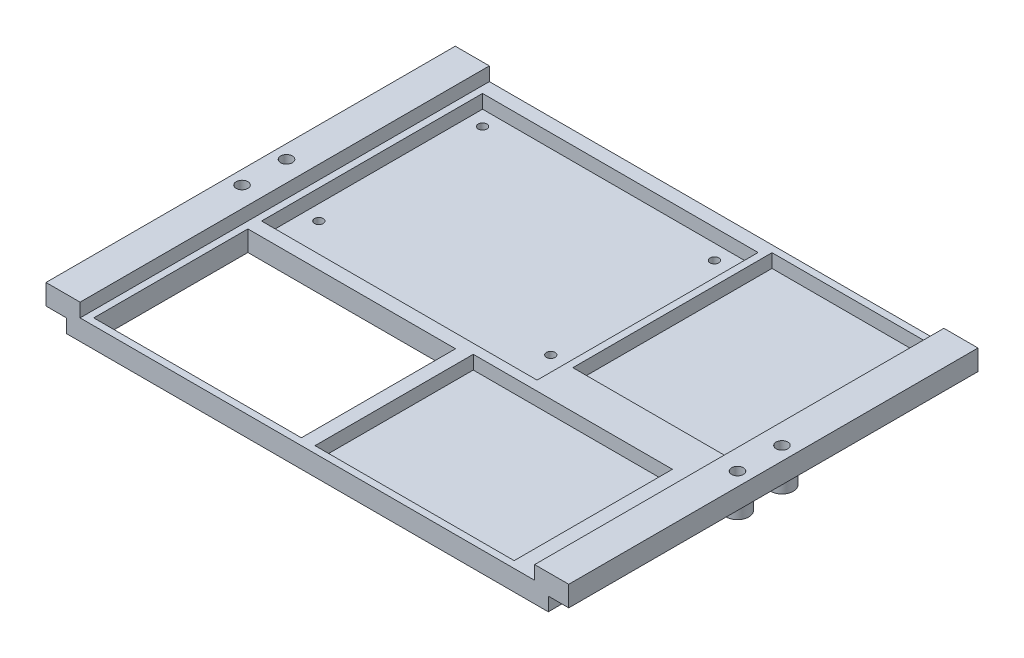
SolidWorks part; units mm, degrees
ref_plane "Front Plane" through (0, 0, 0) normal (0, 0, 1) x (1, 0, 0)
ref_plane "Top Plane" through (0, 0, 0) normal (0, 1, 0) x (1, 0, 0)
ref_plane "Right Plane" through (0, 0, 0) normal (1, 0, 0) x (0, 0, -1)
sketch "Sketch2" plane through (0, 0, 0) normal (0, 0, 1) x (1, 0, 0)
  line L0 (179.1, 12.5) -> (191.6, 12.5)
  line L1 (7.5, 0) -> (184.1, 0)
  line L2 (0, 5) -> (0, 12.5)
  line L3 (0, 12.5) -> (12.5, 12.5)
  line L4 (191.6, 5) -> (191.6, 12.5)
  line L7 (0, 5) -> (7.5, 5)
  line L8 (7.5, 0) -> (7.5, 5)
  line L11 (191.6, 5) -> (184.1, 5)
  line L12 (184.1, 0) -> (184.1, 5)
  line L14 (12.5, 12.5) -> (12.5, 7.5)
  line L15 (12.5, 7.5) -> (179.1, 7.5)
  line L16 (179.1, 12.5) -> (179.1, 7.5)
  dimension "D1" = 191.6
  dimension "D2" = 5
  dimension "D3" = 5
  dimension "D4" = 5
  dimension "D5" = 12.5
  dimension "D6" = 7.5
  dimension "D7" = 7.5
  dimension "D8" = 12.5
  dimension "D9" = 12.5
extrude "PlateFrame" add sketch "Sketch2" along normal blind 150
sketch "Sketch3" plane through (0, 12.5, 0) normal (0, 1, 0) x (1, 0, 0)
  line L0 (12.5, 0) -> (0, 0) construction
  line L2 (0, -150) -> (0, 0) construction
  line L3 (191.6, -150) -> (191.6, 0) construction
  line L4 (191.6, 0) -> (179.1, 0) construction
  circle A0 centre (5, -66.85) radius 2.15
  circle A1 centre (5, -83.15) radius 2.15
  circle A2 centre (186.6, -66.85) radius 2.15
  circle A3 centre (186.6, -83.15) radius 2.15
  dimension "D1" = 4.3
  dimension "D2" = 4.3
  dimension "D3" = 4.3
  dimension "D4" = 4.3
  dimension "D5" = 66.85
  dimension "D6" = 16.3
  dimension "D7" = 5
  dimension "D8" = 5
  dimension "D9" = 5
  dimension "D10" = 181.6
  dimension "D11" = 66.85
  dimension "D12" = 16.3
extrude "HoleSupport" cut sketch "Sketch3" against normal blind 7.5
sketch "Sketch4" plane through (0, 12.5, 0) normal (0, 1, 0) x (1, 0, 0)
  circle A0 centre (5, -66.85) radius 2.15
  circle A1 centre (5, -83.15) radius 2.15
  circle A2 centre (186.6, -83.15) radius 2.15
  circle A3 centre (186.6, -66.85) radius 2.15
  circle A4 centre (186.6, -66.85) radius 4.15
  circle A5 centre (186.6, -83.15) radius 4.15
  circle A6 centre (5, -66.85) radius 4.15
  circle A7 centre (5, -83.15) radius 4.15
  dimension "D1" = 2
extrude "CylindricalSupports" add sketch "Sketch4" against normal blind 12.5
sketch "Sketch5" plane through (0, 7.5, 0) normal (0, 1, 0) x (1, 0, 0)
  line L2 (12.5, -150) -> (12.5, 0) construction
  line L3 (15, -5) -> (116, -5)
  line L4 (15, -5) -> (15, -86)
  line L5 (15, -86) -> (116, -86)
  line L6 (116, -5) -> (116, -86)
  line L7 (176.6, -2.5) -> (118.6, -2.5)
  line L8 (176.6, -2.5) -> (176.6, -75.5)
  line L9 (176.6, -75.5) -> (118.6, -75.5)
  line L10 (118.6, -2.5) -> (118.6, -75.5)
  line L11 (169.1, -147.5) -> (96.1, -147.5)
  line L12 (169.1, -147.5) -> (169.1, -89.5)
  line L13 (169.1, -89.5) -> (96.1, -89.5)
  line L14 (96.1, -147.5) -> (96.1, -89.5)
  line L15 (179.1, -150) -> (179.1, 0) construction
  line L16 (179.1, 0) -> (12.5, 0) construction
  line L17 (179.1, -150) -> (12.5, -150) construction
  dimension "D1" = 2.5
  dimension "D2" = 101
  dimension "D3" = 81
  dimension "D4" = 2.5
  dimension "D5" = 10
  dimension "D6" = 58
  dimension "D7" = 73
  dimension "D8" = 5
  dimension "D9" = 2.5
  dimension "D10" = 2.5
  dimension "D11" = 73
  dimension "D12" = 58
extrude "ItemLayout" cut sketch "Sketch5" against normal blind 5
sketch "Sketch6" plane through (0, 2.5, 0) normal (0, 1, 0) x (1, 0, 0)
  line L14 (15, -86) -> (116, -86) construction
  line L15 (116, -86) -> (116, -5) construction
  line L16 (15, -5) -> (15, -86) construction
  line L17 (15, -5) -> (15, -86) construction
  line L18 (116, -5) -> (15, -5) construction
  circle A0 centre (20.5, -10.5) radius 1.6
  circle A1 centre (20.5, -70.5) radius 1.6
  circle A2 centre (105.5, -70.5) radius 1.6
  circle A3 centre (105.5, -10.5) radius 1.6
  dimension "D1" = 3.2
  dimension "D2" = 3.2
  dimension "D3" = 3.2
  dimension "D4" = 3.2
  dimension "D5" = 15.5
  dimension "D6" = 15.5
  dimension "D7" = 10.5
  dimension "D8" = 5.5
  dimension "D9" = 10.5
  dimension "D11" = 5.5
  dimension "D12" = 5.5
  dimension "D10" = 5.5
extrude "JetsonBaseHoles" cut sketch "Sketch6" against normal blind 2.5
sketch "Sketch7" plane through (0, 7.5, 0) normal (0, 1, 0) x (1, 0, 0)
  line L0 (179.1, -150) -> (12.5, -150) construction
  line L1 (91.1, -147.5) -> (15, -147.5)
  line L2 (91.1, -147.5) -> (91.1, -91)
  line L3 (91.1, -91) -> (15, -91)
  line L4 (15, -147.5) -> (15, -91)
  line L5 (12.5, -150) -> (12.5, 0) construction
  line L6 (15, -86) -> (116, -86) construction
  line L7 (96.1, -89.5) -> (96.1, -147.5) construction
  dimension "D1" = 2.5
  dimension "D2" = 2.5
  dimension "D3" = 5
  dimension "D4" = 5
extrude "OpenHole" cut sketch "Sketch7" against normal through all
